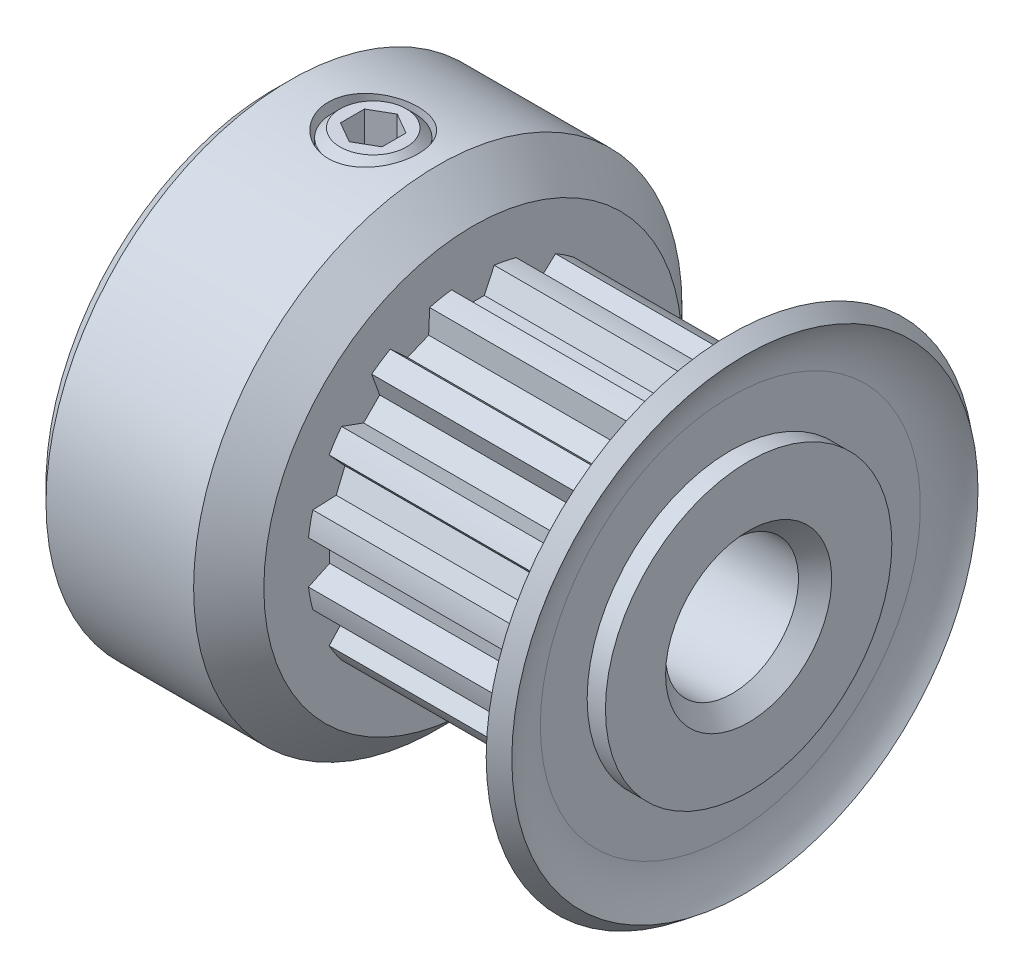
SolidWorks part; units mm, degrees
material "Plain Carbon Steel"
ref_plane "Front Plane" through (0, 0, 0) normal (0, 0, 1) x (1, 0, 0)
ref_plane "Top Plane" through (0, 0, 0) normal (0, 1, 0) x (1, 0, 0)
ref_plane "Right Plane" through (0, 0, 0) normal (1, 0, 0) x (0, 0, -1)
sketch "Sketch2" plane through (0, 0, 0) normal (1, 0, 0) x (0, 0, -1)
  line L3 (0, 0) -> (0, 4.3245) construction
  line L6 (0, -4.8325) -> (0, -5.15) construction
  line L7 (-0.5715, 4.7986) -> (-0.344, 4.3108)
  line L8 (0.5715, 4.7986) -> (0.344, 4.3108)
  line L9 (-0.5715, 4.7986) -> (-0.642, 4.9498)
  line L10 (0.5715, 4.7986) -> (0.642, 4.9498)
  line L12 (-0.344, 4.3108) -> (0.344, 4.3108)
  line L14 (0, 4.8325) -> (0, 5.15) construction
  line L15 (0, 0) -> (0, -1.143) construction
  circle A0 centre (0, 0) radius 5.15 construction
  circle A1 centre (0, 0) radius 4.3245 construction
  circle A2 centre (0, 0) radius 4.8325 construction
  arc A7 (0.642, 4.9498) -> (-0.642, 4.9498) centre (0, 0) ccw
  point P5 (0, 4.9912)
  dimension "D3" = 0.3175
  dimension "D1" = 50
sketch "Sketch1" plane through (0, 0, 0) normal (0, 0, 1) x (1, 0, 0)
  line L0 (-7.15, 0) -> (7.15, 0) construction
  line L1 (-7.15, 2) -> (7.15, 2)
  line L2 (-7.15, 2) -> (-7.15, 7.35)
  line L3 (-7.15, 7.35) -> (-2.207, 7.35)
  line L4 (-2.207, 7.35) -> (-1.15, 6.293)
  line L5 (-1.15, 6.293) -> (-1.15, 5.15)
  line L6 (-1.15, 5.15) -> (6.05, 5.15)
  line L7 (6.05, 5.15) -> (6.05, 5.7215)
  line L8 (6.05, 5.15) -> (7.15, 5.15) construction
  line L9 (6.6, 7.35) -> (7.15, 7.35)
  line L10 (7.15, 7.35) -> (7.15, 2)
  line L11 (6.6, 5.15) -> (6.6, 7.35) construction
  line L12 (-4.6785, 7.35) -> (-4.6785, 2) construction
  arc A0 (6.05, 5.7215) -> (6.6, 7.35) centre (8.7359, 5.7215) cw
  dimension "Bore Size" = 4
  dimension "Overall Width" = 14.3
  dimension "Inside Width" = 7.2
  dimension "Outside Width" = 8.3
  dimension "Hub Dia" = 14.7
  dimension "OD" = 14.7
  dimension "D1" = 45
  dimension "D2" = 10.3
  dimension "D3" = 1.143
  dimension "D4" = 0.5715
revolve "Revolve1" add sketch "Sketch1" angle 360 mid plane about L0
sketch "Sketch4" plane through (-1.15, 0, 0) normal (1, 0, 0) x (0, 0, -1)
  circle A0 centre (0, 0) radius 4.9912
  circle A1 centre (0, 0) radius 5.15 construction
  circle A2 centre (0, 0) radius 5.15
extrude "Cut-Extrude2" cut sketch "Sketch4" along normal up to surface (7.2 mm away) up to face at (6.05, 0, 5.15)
sketch "Sketch3" plane through (-1.15, 0, 0) normal (1, 0, 0) x (0, 0, -1)
  line L2 (-0.5715, 4.7986) -> (-0.344, 4.3108) construction
  line L3 (-0.344, 4.3108) -> (0.344, 4.3108) construction
  line L4 (0.5715, 4.7986) -> (0.344, 4.3108) construction
  line L5 (-0.642, 4.9498) -> (-0.344, 4.3108)
  line L6 (-0.344, 4.3108) -> (0.344, 4.3108)
  line L7 (0.642, 4.9498) -> (0.344, 4.3108)
  arc A1 (0.642, 4.9498) -> (-0.642, 4.9498) centre (0, 0) ccw construction
  arc A2 (0.642, 4.9498) -> (-0.642, 4.9498) centre (0, 0) ccw
extrude "Cut-Extrude1" cut sketch "Sketch3" along normal up to surface (7.2 mm away)
pattern_circular "CirPattern1" count 16 over 360 about axis through (0, 0, 0) along (1, 0, 0) of "Cut-Extrude1"
sketch "Sketch5" plane through (0, 0, 0) normal (0, 1, 0) x (1, 0, 0)
  line L0 (-7.15, 7.35) -> (-7.15, -7.35) construction
  line L1 (6.05, 5.7215) -> (6.05, -5.7215) construction
  line L2 (7.15, 7.35) -> (7.15, -7.35) construction
  line L3 (-1.15, 6.293) -> (-1.15, -6.293) construction
  line L4 (6.05, 5.7215) -> (6.05, -5.7215) construction
  line L5 (-7.15, 0) -> (7.15, 0) construction
  line L6 (-7.15, 0) -> (7.15, 0) construction
  point P0 (6.05, 0)
  point P14 (6.05, 0)
  point P15 (-1.15, 0)
  dimension "D1" = 14.7
  dimension "D2" = 14.7
sketch "Sketch6" plane through (0, 0, 0) normal (0, 1, 0) x (1, 0, 0)
  line L0 (-7.15, 0) -> (-5.4, 0) construction
  line L1 (-7.15, 7.35) -> (-7.15, -7.35) construction
  line L2 (-1.15, 0) -> (-2.9, 0) construction
  line L3 (-1.15, -0.344) -> (-1.15, 0.344) construction
  line L4 (-5.4, 0) -> (-4.15, 0) construction
  line L5 (-4.15, 0) -> (-5.0339, -0.8839) construction
  circle A0 centre (-4.15, 0) radius 1.25 construction
  circle A1 centre (-4.15, 0) radius 1.35
  point P13 (-5.0339, -0.8839)
  dimension "D1" = 0.1
  dimension "D2" = 45
  dimension "SS Dia" = 2.5
extrude "Cut-Extrude3" cut sketch "Sketch6" along normal through all
sketch "Sketch7" plane through (0, 0, 0) normal (0, 0, 1) x (1, 0, 0)
  line L0 (-5.146, 7.35) -> (-4.15, 7.35)
  line L1 (-5.4, 7.096) -> (-5.4, 2.635)
  line L2 (-5.4, 2.635) -> (-5.146, 2.381)
  line L3 (-5.146, 2.381) -> (-4.15, 2.381)
  line L4 (-4.15, 2.381) -> (-4.15, 7.35) construction
  line L6 (-5.4, 7.096) -> (-5.146, 7.35)
  line L7 (-7.15, 7.35) -> (-2.207, 7.35) construction
  line L8 (-4.15, 7.35) -> (-4.15, 2.381)
  point P0 (-5.4, 7.35)
  point P4 (-5.4, 2.381)
  dimension "D2" = 0.381
revolve "Revolve2" add sketch "Sketch7" angle 360 mid plane about L4
sketch "Sketch8" plane through (0, 7.35, 0) normal (0, 1, 0) x (1, 0, 0)
  line L0 (-4.15, 0) -> (-5.4, 0) construction
  line L1 (-4.15, 0.7217) -> (-4.775, 0.3608)
  line L2 (-4.775, 0.3608) -> (-4.775, -0.3608)
  line L3 (-4.775, -0.3608) -> (-4.15, -0.7217)
  line L4 (-4.15, -0.7217) -> (-3.525, -0.3608)
  line L5 (-3.525, -0.3608) -> (-3.525, 0.3608)
  line L6 (-3.525, 0.3608) -> (-4.15, 0.7217)
  circle A0 centre (-4.15, 0) radius 0.625 construction
  point P13 (-4.775, 0)
extrude "Cut-Extrude4" cut sketch "Sketch8" against normal blind 1.016
pattern_circular "CirPattern2" [suppressed] count 2 over 90
pattern_circular "CirPattern3" [suppressed] count 2 over 90
chamfer "Chamfer1" distance 0.5 angle 45 3 edges at (-7.15, 0, 7.35) (-7.15, 0, 2) (7.15, 0, 2)
sketch "Sketch9" plane through (0, 0, 0) normal (0, 0, 1) x (1, 0, 0)
  line L0 (7.15, 4.3108) -> (7.15, 7.35)
  line L1 (7.15, 7.35) -> (7.15, 2) construction
  line L2 (6.6, 5.15) -> (6.6, 7.35) construction
  line L3 (6.6, 5.7215) -> (6.6, 4.3108)
  line L4 (6.6, 7.35) -> (6.8022, 7.6152)
  line L5 (6.6, 4.3108) -> (7.15, 4.3108)
  line L6 (6.6, 7.35) -> (7.0374, 7.0165)
  line L7 (6.8022, 7.6152) -> (7.15, 7.35)
  line L8 (-1.15, 4.3108) -> (7.15, 4.3108) construction
  line L9 (-7.15, 0) -> (7.15, 0) construction
  line L10 (-7.15, 0) -> (7.15, 0) construction
  arc A0 (6.6, 7.35) -> (6.05, 5.7215) centre (8.7359, 5.7215) ccw construction
  arc A3 (6.6, 5.7215) -> (7.0374, 7.0165) centre (8.7359, 5.7215) cw
revolve "Cut-Revolve1" cut sketch "Sketch9" angle 360 about L0
equation "\"D3@Sketch2\" = (\"hs@Sketch2\"-\"ht@Sketch2\")/2"
equation "\"D2@Sketch1\" = \"PD@Sketch2\""
equation "\"D3@Sketch1\" = \"hs@Sketch2\""
equation "\"D4@Sketch1\" = \"D3@Sketch1\"/2"
equation "\"D1@Sketch5\"=\"Hub Dia@Sketch1\""
equation "\"D2@Sketch5\"=\"OD@Sketch1\""
